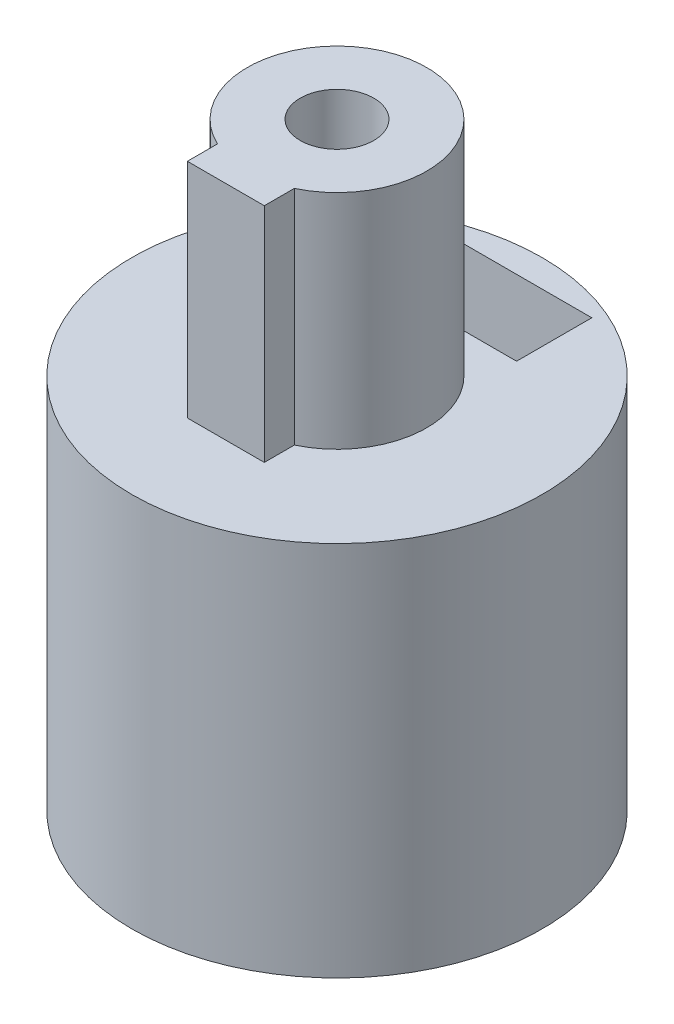
SolidWorks part; units mm, degrees
ref_plane "Front Plane" through (0, 0, 0) normal (0, 0, 1) x (1, 0, 0)
ref_plane "Top Plane" through (0, 0, 0) normal (0, 1, 0) x (1, 0, 0)
ref_plane "Right Plane" through (0, 0, 0) normal (1, 0, 0) x (0, 0, -1)
sketch "Sketch1" plane through (0, 0, 0) normal (0, 1, 0) x (1, 0, 0)
  circle A0 centre (0, 0) radius 1.965 construction
  circle A1 centre (0, 0) radius 6
  dimension "D1" = 3.93
  dimension "D2" = 12
extrude "Boss-Extrude1" add sketch "Sketch1" along normal blind 10
sketch "Sketch2" plane through (0, 0, 0) normal (0, 0, 1) x (1, 0, 0)
  line L0 (0, 10) -> (0, 0) construction
  line L1 (6, 10) -> (-6, 10) construction
  circle A0 centre (0, 7) radius 1.025
  dimension "D1" = 2.05
  dimension "D2" = 3
extrude "Cut-Extrude1" cut sketch "Sketch2" against normal through all
sketch "Sketch4" plane through (0, 0, 0) normal (0, 1, 0) x (1, 0, 0)
  circle A0 centre (0, 0) radius 2.275
  dimension "D1" = 4.55
extrude "Cut-Extrude4" cut sketch "Sketch4" along normal through all
sketch "Sketch5" plane through (0, 10, 0) normal (0, 1, 0) x (1, 0, 0)
  line L0 (-6, 0) -> (6, 0) construction
  line L2 (-0.475, -3.5346) -> (0.475, -3.5346)
  line L3 (-0.475, -3.5346) -> (-0.475, 3.5346)
  line L4 (-0.475, 3.5346) -> (0.475, 3.5346)
  line L5 (0.475, -3.5346) -> (0.475, 3.5346)
  line L6 (0, 3.5346) -> (0, -3.5346) construction
  line L7 (-0.475, 0) -> (0.475, 0) construction
  circle A0 centre (0, 0) radius 6 construction
  point P5 (0, 0)
  dimension "D1" = 0.95
extrude "Boss-Extrude2" add sketch "Sketch5" against normal blind 1.2
sketch "Sketch7" plane through (0, 10, 0) normal (0, 1, 0) x (1, 0, 0)
  circle A0 centre (0, 0) radius 6
  circle A1 centre (0, 0) radius 6 construction
extrude "Boss-Extrude3" add sketch "Sketch7" along normal blind 1
sketch "Sketch8" plane through (0, 11, 0) normal (0, 1, 0) x (1, 0, 0)
  line L0 (0, 0) -> (0, -6) construction
  line L2 (-1.125, -2) -> (1.125, -2)
  line L3 (-1.125, -2) -> (-1.125, -3.25)
  line L4 (-1.125, -3.25) -> (1.125, -3.25)
  line L5 (1.125, -2) -> (1.125, -3.25)
  line L6 (0, -3.25) -> (0, -2) construction
  line L7 (-1.125, -2.625) -> (1.125, -2.625) construction
  circle A0 centre (0, 0) radius 2.625
  circle A1 centre (0, 0) radius 6 construction
  point P3 (0, -2.625)
  dimension "D1" = 5.25
  dimension "D2" = 3.25
  dimension "D3" = 2.25
extrude "Boss-Extrude4" add sketch "Sketch8" along normal blind 6.5 contours A0 L3 L4 L5
sketch "Sketch9" plane through (0, 17.5, 0) normal (0, 1, 0) x (1, 0, 0)
  circle A0 centre (0, 0) radius 1.075
  dimension "D1" = 2.15
extrude "Cut-Extrude5" cut sketch "Sketch9" against normal blind 6
sketch "Sketch3" plane through (0, 0, 0) normal (0, 0, 1) x (1, 0, 0)
  line L1 (0, 4.4019) -> (2.25, 5.701)
  line L2 (2.25, 5.701) -> (2.25, 8.299)
  line L3 (2.25, 8.299) -> (0, 9.5981) construction
  line L4 (0, 9.5981) -> (-2.25, 8.299) construction
  line L5 (-2.25, 8.299) -> (-2.25, 5.701)
  line L6 (-2.25, 5.701) -> (0, 4.4019)
  line L10 (-2.25, 8.299) -> (2.25, 8.299) construction
  line L11 (-2.25, 8.299) -> (-2.25, 11.4728)
  line L12 (2.25, 8.299) -> (2.25, 11.4728)
  line L13 (-2.25, 11.4728) -> (2.25, 11.4728)
  circle A0 centre (0, 7) radius 2.25 construction
  dimension "D1" = 4.5
extrude "Cut-Extrude2" cut sketch "Sketch3" against normal blind 2.2 from offset 3
